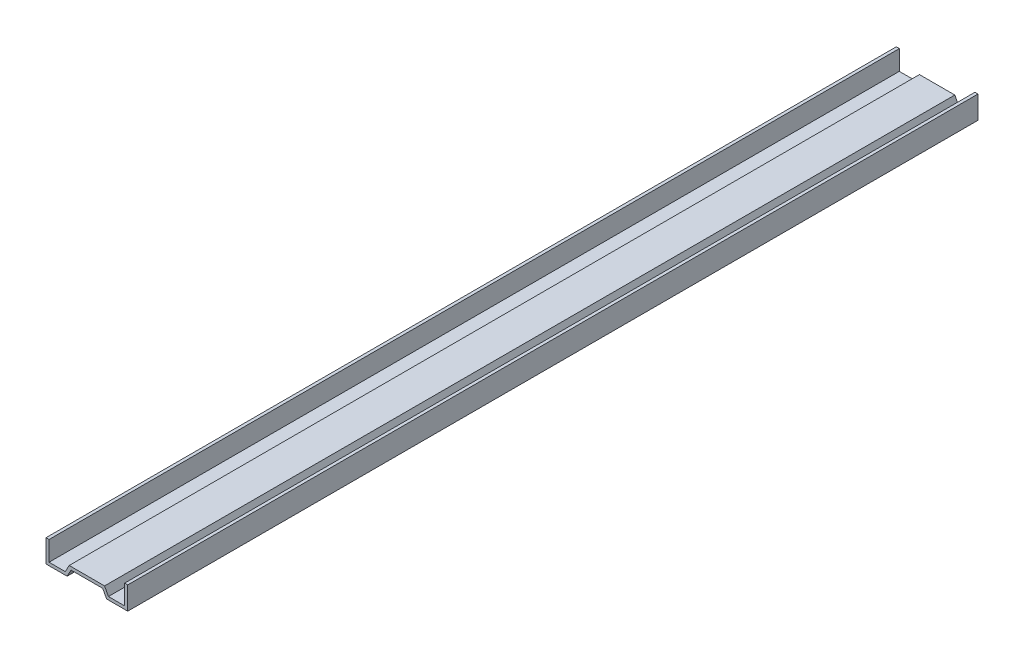
SolidWorks part; units mm, degrees
ref_plane "Front Plane" through (0, 0, 0) normal (0, 0, 1) x (1, 0, 0)
ref_plane "Top Plane" through (0, 0, 0) normal (0, 1, 0) x (1, 0, 0)
ref_plane "Right Plane" through (0, 0, 0) normal (1, 0, 0) x (0, 0, -1)
ref_plane "Plane1" through (0, 0, 362) normal (0, 0, 1) x (1, 0, 0)
sketch "Sketch1" plane through (0, 0, 362) normal (0, 0, 1) x (1, 0, 0)
  line L0 (-9.1805, -3.0955) -> (-16.1, -3.0955)
  line L1 (-16.1, -3.0955) -> (-16.1, 5.3045)
  line L2 (-16.1, 5.3045) -> (-17.4, 5.3045)
  line L3 (-17.4, 5.3045) -> (-17.4, -4.3955)
  line L4 (-17.4, -4.3955) -> (-8.4, -4.3955)
  line L5 (-8.4, -4.3955) -> (-6.7499, -1.3)
  line L6 (-6.7499, -1.3) -> (6.7501, -1.3)
  line L7 (6.7501, -1.3) -> (8.4, -4.3955)
  line L8 (8.4, -4.3955) -> (17.4, -4.3955)
  line L9 (17.4, -4.3955) -> (17.4, 5.3045)
  line L10 (17.4, 5.3045) -> (16.1, 5.3045)
  line L11 (16.1, 5.3045) -> (16.1, -3.0955)
  line L12 (16.1, -3.0955) -> (9.1802, -3.0955)
  line L13 (9.1802, -3.0955) -> (7.5303, 0)
  line L14 (7.5303, 0) -> (-7.5303, 0)
  line L15 (-7.5303, 0) -> (-9.1805, -3.0955)
extrude "Boss-Extrude1" add sketch "Sketch1" against normal blind 362
scale "Scale1" scale about centroid uniform scaling yes scale factor 0.25
